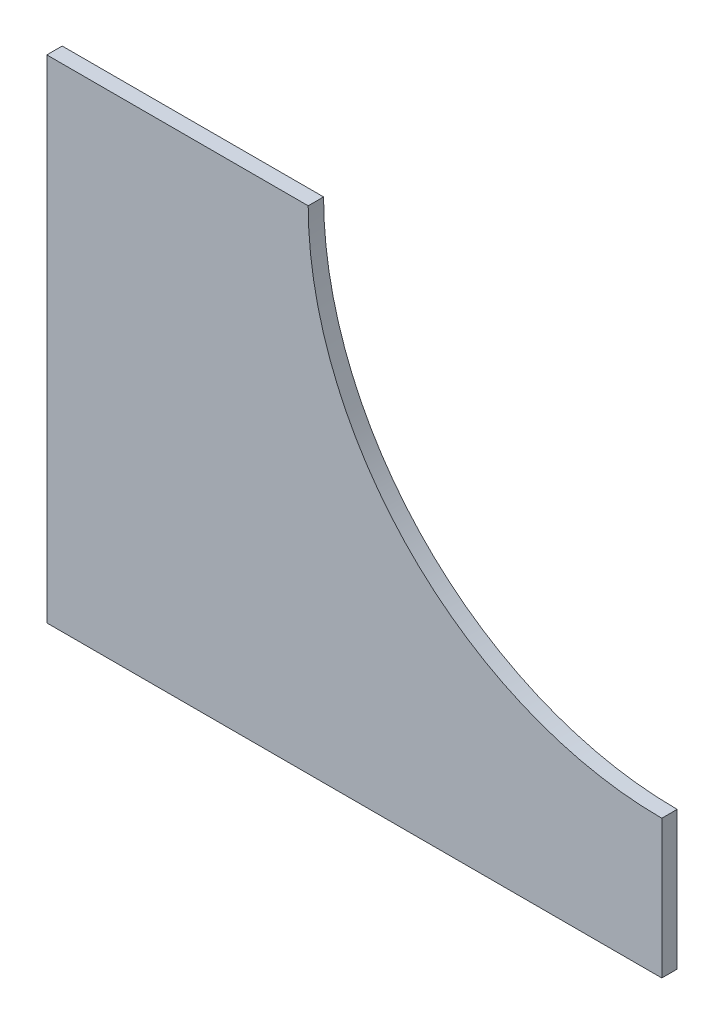
SolidWorks part; units mm, degrees
material "6061-T6 (SS)"
ref_plane "Front Plane" through (0, 0, 0) normal (0, 0, 1) x (1, 0, 0)
ref_plane "Top Plane" through (0, 0, 0) normal (0, 1, 0) x (1, 0, 0)
ref_plane "Right Plane" through (0, 0, 0) normal (1, 0, 0) x (0, 0, -1)
sketch "Sketch1" plane through (0, 0, 0) normal (0, 0, 1) x (1, 0, 0)
  line L0 (98.4295, -196.655) -> (98.4295, -225.23)
  line L1 (98.4295, -225.23) -> (-28.5705, -225.23)
  line L2 (-28.5705, -225.23) -> (-28.5705, -123.63)
  line L4 (-28.5705, -123.63) -> (25.4045, -123.63)
  line L5 (98.4295, -196.655) -> (73.0295, -196.655) construction
  arc A0 (98.4295, -196.655) -> (25.4045, -123.63) centre (98.4295, -123.63) cw
  dimension "D4" = 73.025
  dimension "D1" = 101.6
  dimension "D2" = 28.575
  dimension "D3" = 127
  dimension "D5" = 25.4
extrude "Boss-Extrude1" add sketch "Sketch1" along normal blind 3.175
